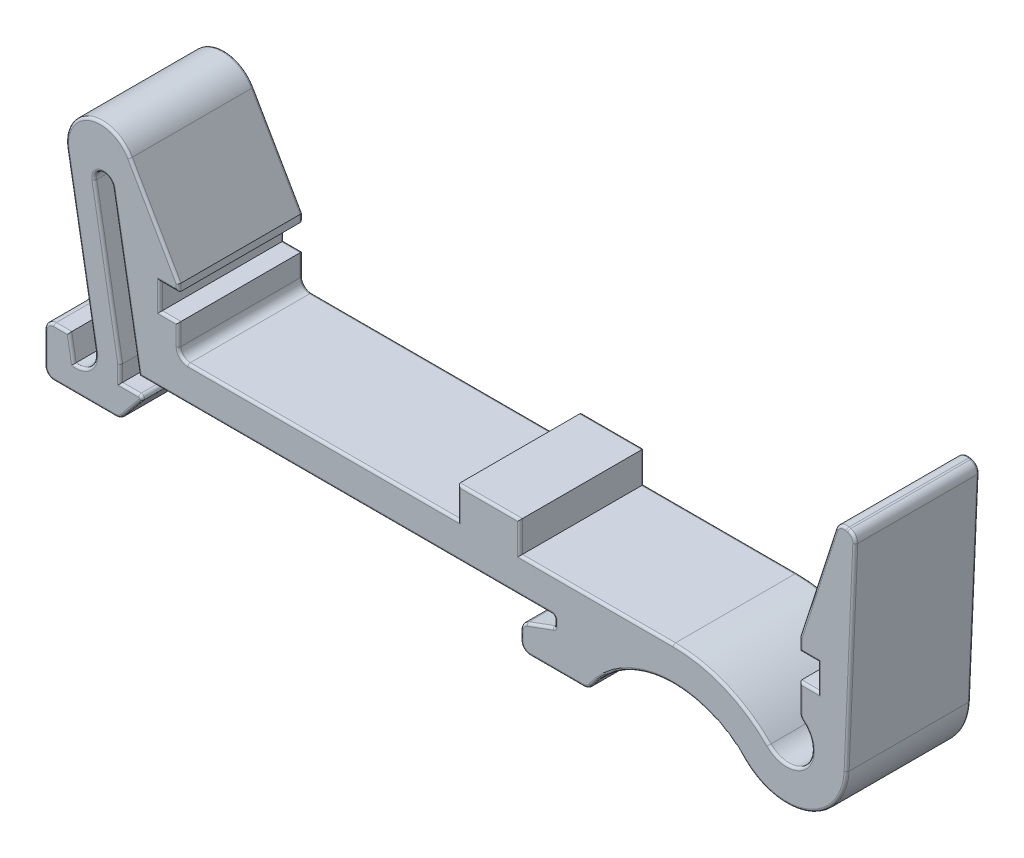
SolidWorks part; units mm, degrees
ref_plane "Front Plane" through (0, 0, 0) normal (0, 0, 1) x (1, 0, 0)
ref_plane "Top Plane" through (0, 0, 0) normal (0, 1, 0) x (1, 0, 0)
ref_plane "Right Plane" through (0, 0, 0) normal (1, 0, 0) x (0, 0, -1)
sketch "Sketch1" plane through (0, 0, 0) normal (0, 0, 1) x (1, 0, 0)
  line L0 (-4.297, 0.2) -> (-5.547, 0.2)
  line L1 (-4.297, 0.2) -> (-3.9443, -1.8)
  line L2 (-6.297, -0.55) -> (-6.297, -3.05)
  line L3 (-5.547, -3.8) -> (-0.5764, -3.8)
  line L4 (0.0036, -3.5255) -> (1.4933, -1.7085)
  line L6 (1.3, -1.3) -> (-0.2, -1.3)
  line L7 (-0.2, -1.3) -> (-0.2, 0)
  line L8 (-0.2, 0) -> (-2.2838, 11.8177)
  line L9 (-0.8066, 12.0782) -> (1.3231, 0)
  line L10 (1.3231, 0) -> (34.55, 0)
  line L13 (34.8, -0.25) -> (34.8, -0.6249)
  line L14 (34.6355, -0.8599) -> (32.5435, -1.6213)
  line L15 (32.05, -2.3261) -> (32.05, -3.0509)
  line L16 (32.8, -3.8009) -> (37.095, -3.8009)
  line L17 (58.3091, 0.8288) -> (59.0111, 17.0699)
  line L18 (57.405, 17.3718) -> (54.5, 8.3666)
  line L19 (54.5, 8.3666) -> (54.5, 7.4)
  line L20 (54.5, 7.4) -> (56, 7.4)
  line L21 (56, 7.4) -> (56, 5.3)
  line L22 (56, 5.3) -> (54.5, 5.3)
  line L23 (54.5, 5.3) -> (54.5, 3.1885)
  line L24 (44.3362, 2.8) -> (5.25, 2.8)
  line L25 (4.5, 3.55) -> (4.5, 5.3)
  line L26 (4.5, 5.3) -> (3, 5.3)
  line L27 (3, 5.3) -> (3, 7.4)
  line L28 (3, 7.4) -> (4.5, 7.4)
  line L29 (4.5, 7.4) -> (4.5, 7.973)
  line L30 (4.5, 7.973) -> (0.5786, 14.7955)
  line L31 (-4.5139, 12.9476) -> (-2.2309, 0)
  line L35 (58.3118, 17.8654) -> (58.4559, 17.8268)
  arc A0 (-5.547, 0.2) -> (-6.297, -0.55) centre (-5.547, -0.55) ccw
  arc A1 (-6.297, -3.05) -> (-5.547, -3.8) centre (-5.547, -3.05) ccw
  arc A2 (-0.5764, -3.8) -> (0.0036, -3.5255) centre (-0.5764, -3.05) ccw
  arc A3 (1.4933, -1.7085) -> (1.3, -1.3) centre (1.3, -1.55) ccw
  arc A4 (-2.2838, 11.8177) -> (-0.8066, 12.0782) centre (-1.5452, 11.9479) cw
  arc A5 (34.55, 0) -> (34.8, -0.25) centre (34.55, -0.25) cw
  arc A6 (34.8, -0.6249) -> (34.6355, -0.8599) centre (34.55, -0.6249) cw
  arc A7 (32.5435, -1.6213) -> (32.05, -2.3261) centre (32.8, -2.3261) ccw
  arc A8 (32.05, -3.0509) -> (32.8, -3.8009) centre (32.8, -3.0509) ccw
  arc A9 (37.095, -3.8009) -> (37.7123, -3.4769) centre (37.095, -3.0509) ccw
  arc A10 (37.7123, -3.4769) -> (50.0435, -2.3738) centre (44.3362, -8.0481) cw
  arc A11 (50.0435, -2.3738) -> (58.3091, 0.8288) centre (53.4749, 1.0378) ccw
  arc A12 (59.0111, 17.0699) -> (58.4559, 17.8268) centre (58.2618, 17.1023) ccw
  arc A13 (58.3118, 17.8654) -> (57.405, 17.3718) centre (58.1179, 17.1418) ccw
  arc A14 (54.5, 3.1885) -> (54.7726, 2.6101) centre (55.25, 3.1885) ccw
  arc A15 (54.7726, 2.6101) -> (52.0291, -0.3996) centre (53.4749, 1.0378) cw
  arc A16 (44.3362, 2.8) -> (52.0291, -0.3996) centre (44.3362, -8.0481) cw
  arc A17 (5.25, 2.8) -> (4.5, 3.55) centre (5.25, 3.55) cw
  arc A18 (0.5786, 14.7955) -> (-4.5139, 12.9476) centre (-1.8056, 13.4251) ccw
  arc A19 (-2.2309, 0) -> (-3.9443, -1.8) centre (-3.7514, -0.2681) cw
  dimension "D3" = 1.5
  dimension "D1" = 35
  dimension "D2" = 53
extrude "Boss-Extrude1" add sketch "Sketch1" along normal blind 10
sketch "Sketch2" plane through (0, 0, 0) normal (0, 0, 1) x (1, 0, 0)
  line L0 (44.3362, 2.8) -> (5.25, 2.8) construction
  line L1 (27, 5.3) -> (32, 5.3)
  line L2 (27, 5.3) -> (27, 2.8)
  line L3 (27, 2.8) -> (32, 2.8)
  line L4 (32, 5.3) -> (32, 2.8)
  line L5 (4.5, 5.3) -> (3, 5.3) construction
  line L6 (3, 6.35) -> (56, 6.35) construction
  line L7 (3, 5.3) -> (3, 7.4) construction
  line L8 (56, 7.4) -> (56, 5.3) construction
  line L9 (29.5, 5.3) -> (29.5, 6.35) construction
  dimension "D1" = 5
extrude "Boss-Extrude2" add sketch "Sketch2" along normal up to surface (10 mm away) up to face at (23.1736, 3.2719, 10)
fillet "Fillet1" radius 0.2 108 edges at (-4.922, 0.2, 0) (-6.0773, -0.0197, 0) (-6.297, -1.8, 0) (-6.0773, -3.5803, 0) (-3.0617, -3.8, 0) (-0.2556, -3.7279, 0) (0.7485, -2.617, 0) (1.526, -1.4431, 0) (0.55, -1.3, 0) (-0.2, -0.65, 0) (-1.2419, 5.9088, 0) (-1.6754, 12.6865, 0) (0.2583, 6.0391, 0) (17.9366, 0, 0) (34.7268, -0.0732, 0) (34.8, -0.4375, 0) (34.7548, -0.7683, 0) (33.5895, -1.2406, 0) (32.1856, -1.8959, 0) (32.05, -2.6885, 0) (32.2697, -3.5812, 0) (34.9475, -3.8009, 0) (37.4436, -3.715, 0) (43.6191, -0.032, 0) (55.2231, -3.4741, 0) (58.6601, 8.9494, 0) (58.8665, 17.5459, 0) (58.3838, 17.8461, 0) (57.7598, 17.7998, 0) (55.9525, 12.8692, 0) (54.5, 7.8833, 0) (55.25, 7.4, 0) (56, 6.35, 0) (55.25, 5.3, 0) (54.5, 4.2443, 0) (54.5716, 2.8688, 0) (54.9816, -0.3356, 0) (48.5021, 1.9682, 0) (16.125, 2.8, 0) (38.1681, 2.8, 0) (4.7197, 3.0197, 0) (4.5, 4.425, 0) (3.75, 5.3, 0) (3, 6.35, 0) (3.75, 7.4, 0) (4.5, 7.6865, 0) (2.5393, 11.3843, 0) (-2.7437, 16.0102, 0) (-3.3724, 6.4738, 0) (-2.6331, -1.3327, 0) (-4.1206, -0.8, 0) (-2.6331, -1.3327, 10) (-3.3724, 6.4738, 10) (-2.7437, 16.0102, 10) (2.5393, 11.3843, 10) (4.5, 7.6865, 10) (3.75, 7.4, 10) (3, 6.35, 10) (3.75, 5.3, 10) (4.5, 4.425, 10) (4.7197, 3.0197, 10) (38.1681, 2.8, 10) (16.125, 2.8, 10) (48.5021, 1.9682, 10) (54.9816, -0.3356, 10) (54.5716, 2.8688, 10) (54.5, 4.2443, 10) (55.25, 5.3, 10) (56, 6.35, 10) (55.25, 7.4, 10) (54.5, 7.8833, 10) (55.9525, 12.8692, 10) (57.7598, 17.7998, 10) (58.3838, 17.8461, 10) (58.8665, 17.5459, 10) (58.6601, 8.9494, 10) (55.2231, -3.4741, 10) (43.6191, -0.032, 10) (37.4436, -3.715, 10) (34.9475, -3.8009, 10) (32.2697, -3.5812, 10) (32.05, -2.6885, 10) (32.1856, -1.8959, 10) (33.5895, -1.2406, 10) (34.7548, -0.7683, 10) (34.8, -0.4375, 10) (34.7268, -0.0732, 10) (17.9366, 0, 10) (0.2583, 6.0391, 10) (-1.6754, 12.6865, 10) (-1.2419, 5.9088, 10) (-0.2, -0.65, 10) (0.55, -1.3, 10) (1.526, -1.4431, 10) (0.7485, -2.617, 10) (-0.2556, -3.7279, 10) (-3.0617, -3.8, 10) (-6.0773, -3.5803, 10) (-6.297, -1.8, 10) (-6.0773, -0.0197, 10) (-4.922, 0.2, 10) (-4.1206, -0.8, 10) (32, 4.05, 10) (32, 4.05, 0) (29.5, 5.3, 10) (29.5, 5.3, 0) (27, 4.05, 10) (27, 4.05, 0)
